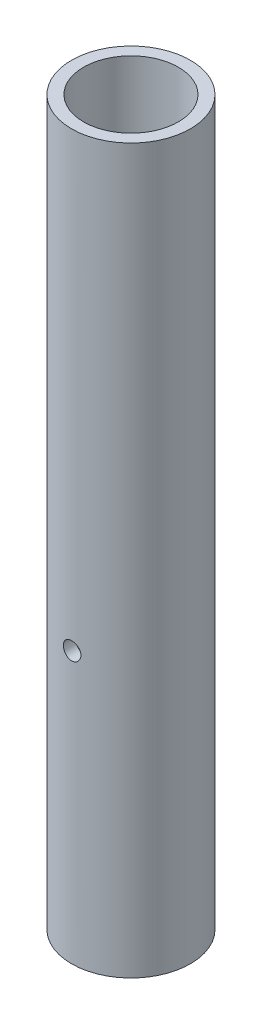
SolidWorks part; units mm, degrees
material "6061 Alloy"
ref_plane "Front Plane" through (0, 0, 0) normal (0, 0, 1) x (1, 0, 0)
ref_plane "Top Plane" through (0, 0, 0) normal (0, 1, 0) x (1, 0, 0)
ref_plane "Right Plane" through (0, 0, 0) normal (1, 0, 0) x (0, 0, -1)
sketch "Sketch1" plane through (0, 0, 0) normal (0, 1, 0) x (1, 0, 0)
  circle A0 centre (0, 0) radius 16.7005
  circle A1 centre (0, 0) radius 13.3223
  dimension "D1" = 33.401
  dimension "D2" = 26.6446
extrude "Boss-Extrude1" add sketch "Sketch1" along normal blind 203.2
ref_plane "Plane1" through (0, 0, 16.7005) normal (0, 0, 1) x (1, 0, 0)
hole_wizard "#10 (0.1935) Diameter Hole1" positions "Sketch2" profile "Sketch3" hole size "#10" standard "ANSI Inch" end condition through all
sketch "Sketch2" plane through (0, 0, 16.7005) normal (0, 0, 1) x (1, 0, 0)
  line L0 (-16.7005, 0) -> (16.7005, 0) construction
  point P0 (0, 76.2)
  dimension "D1" = 76.2
sketch "Sketch3" plane through (0, 76.2, 16.7005) normal (1, 0, 0) x (0, -1, 0)
  line L0 (0, 0) -> (0, 33.401)
  line L1 (0, 33.401) -> (2.4574, 33.401)
  line L2 (2.4574, 33.401) -> (2.4574, 0)
  line L5 (2.4574, 0) -> (0, 0)
  line L11 (0, -6.35) -> (0, 107.95) construction
  dimension "Thru Hole Dia." = 4.9149
  dimension "Thru Hole Depth" = 33.401
